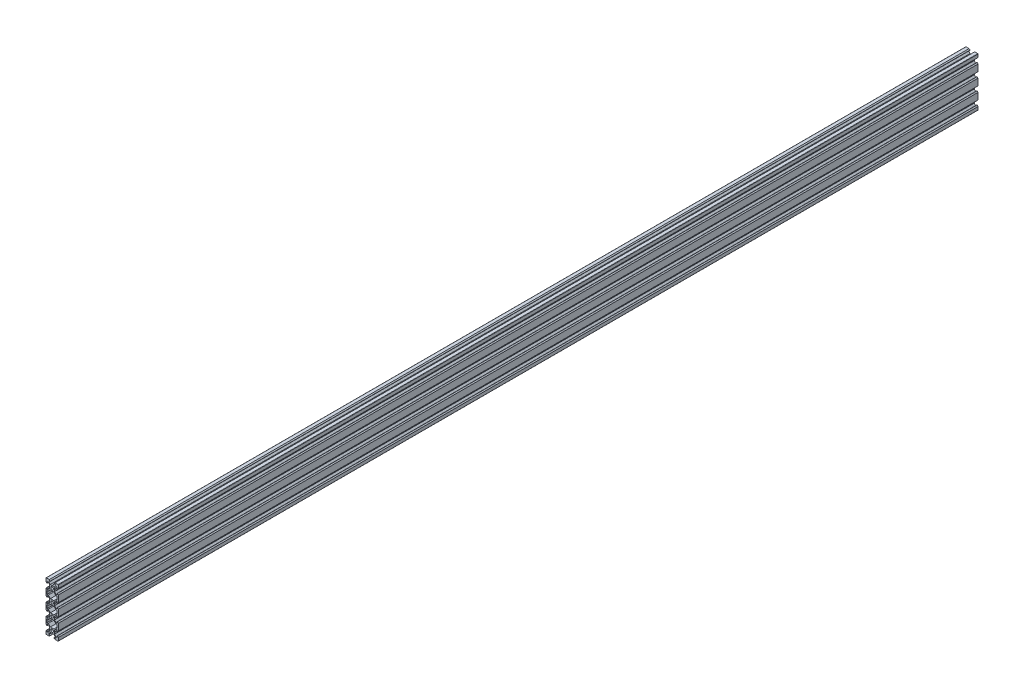
SolidWorks part; units mm, degrees
material "6061-T6 (SS)"
ref_plane "Front Plane" through (0, 0, 0) normal (0, 0, 1) x (1, 0, 0)
ref_plane "Top Plane" through (0, 0, 0) normal (0, 1, 0) x (1, 0, 0)
ref_plane "Right Plane" through (0, 0, 0) normal (1, 0, 0) x (0, 0, -1)
sketch "Sketch1" plane through (0, 0, 0) normal (0, 0, 1) x (1, 0, 0)
  line L0 (0, 0) -> (10, 0) construction
  line L1 (9.5, -40) -> (-9.5, -40)
  line L2 (10, -39.5) -> (10, 39.5)
  line L3 (9.5, 40) -> (-9.5, 40)
  line L4 (-10, -39.5) -> (-10, 39.5)
  line L5 (10, -40) -> (-10, 40) construction
  line L6 (10, 40) -> (-10, -40) construction
  circle A0 centre (0, 30) radius 2.1
  circle A1 centre (0, 10) radius 2.1
  circle A2 centre (0, -10) radius 2.1
  circle A3 centre (0, -30) radius 2.1
  arc A4 (-9.5, -40) -> (-10, -39.5) centre (-9.5, -39.5) cw
  arc A5 (9.5, -40) -> (10, -39.5) centre (9.5, -39.5) ccw
  arc A6 (10, 39.5) -> (9.5, 40) centre (9.5, 39.5) ccw
  arc A7 (-9.5, 40) -> (-10, 39.5) centre (-9.5, 39.5) ccw
  point P0 (0, 0)
  line B0 (0, 30) -> (0, 40) construction
  line B1 (0, 33.69) -> (-0.21, 33.9)
  line B2 (-0.21, 33.9) -> (-2.8393, 33.9)
  line B3 (-2.8393, 33.9) -> (-5.5, 36.5607)
  line B4 (-5.5, 36.5607) -> (-5.5, 38.2)
  line B5 (-5.5, 38.2) -> (-3.125, 38.2)
  line B6 (-3.125, 38.2) -> (-3.125, 38.545)
  line B7 (-3.125, 38.545) -> (-4.58, 40)
  line B8 (-4.58, 40) -> (4.58, 40)
  line B9 (0, 30) -> (-5.9132, 35.9132) construction
  line B10 (3.125, 38.545) -> (4.58, 40)
  line B11 (3.125, 38.2) -> (3.125, 38.545)
  line B12 (5.5, 38.2) -> (3.125, 38.2)
  line B13 (5.5, 36.5607) -> (5.5, 38.2)
  line B14 (2.8393, 33.9) -> (5.5, 36.5607)
  line B15 (0.21, 33.9) -> (2.8393, 33.9)
  line B16 (0, 33.69) -> (0.21, 33.9)
  line B17 (0, 30) -> (-10, 30) construction
  line B18 (-3.69, 30) -> (-3.9, 29.79)
  line B19 (-3.9, 29.79) -> (-3.9, 27.1607)
  line B20 (-3.9, 27.1607) -> (-6.5607, 24.5)
  line B21 (-6.5607, 24.5) -> (-8.2, 24.5)
  line B22 (-8.2, 24.5) -> (-8.2, 26.875)
  line B23 (-8.2, 26.875) -> (-8.545, 26.875)
  line B24 (-8.545, 26.875) -> (-10, 25.42)
  line B25 (-10, 25.42) -> (-10, 34.58)
  line B26 (0, 30) -> (-5.9132, 24.0868) construction
  line B27 (-8.545, 33.125) -> (-10, 34.58)
  line B28 (-8.2, 33.125) -> (-8.545, 33.125)
  line B29 (-8.2, 35.5) -> (-8.2, 33.125)
  line B30 (-6.5607, 35.5) -> (-8.2, 35.5)
  line B31 (-3.9, 32.8393) -> (-6.5607, 35.5)
  line B32 (-3.9, 30.21) -> (-3.9, 32.8393)
  line B33 (-3.69, 30) -> (-3.9, 30.21)
  line B34 (0, 10) -> (-10, 10) construction
  line B35 (-3.69, 10) -> (-3.9, 9.79)
  line B36 (-3.9, 9.79) -> (-3.9, 7.1607)
  line B37 (-3.9, 7.1607) -> (-6.5607, 4.5)
  line B38 (-6.5607, 4.5) -> (-8.2, 4.5)
  line B39 (-8.2, 4.5) -> (-8.2, 6.875)
  line B40 (-8.2, 6.875) -> (-8.545, 6.875)
  line B41 (-8.545, 6.875) -> (-10, 5.42)
  line B42 (-10, 5.42) -> (-10, 14.58)
  line B43 (0, 10) -> (-5.9132, 4.0868) construction
  line B44 (-8.545, 13.125) -> (-10, 14.58)
  line B45 (-8.2, 13.125) -> (-8.545, 13.125)
  line B46 (-8.2, 15.5) -> (-8.2, 13.125)
  line B47 (-6.5607, 15.5) -> (-8.2, 15.5)
  line B48 (-3.9, 12.8393) -> (-6.5607, 15.5)
  line B49 (-3.9, 10.21) -> (-3.9, 12.8393)
  line B50 (-3.69, 10) -> (-3.9, 10.21)
  line B51 (0, -10) -> (-10, -10) construction
  line B52 (-3.69, -10) -> (-3.9, -10.21)
  line B53 (-3.9, -10.21) -> (-3.9, -12.8393)
  line B54 (-3.9, -12.8393) -> (-6.5607, -15.5)
  line B55 (-6.5607, -15.5) -> (-8.2, -15.5)
  line B56 (-8.2, -15.5) -> (-8.2, -13.125)
  line B57 (-8.2, -13.125) -> (-8.545, -13.125)
  line B58 (-8.545, -13.125) -> (-10, -14.58)
  line B59 (-10, -14.58) -> (-10, -5.42)
  line B60 (0, -10) -> (-5.9132, -15.9132) construction
  line B61 (-8.545, -6.875) -> (-10, -5.42)
  line B62 (-8.2, -6.875) -> (-8.545, -6.875)
  line B63 (-8.2, -4.5) -> (-8.2, -6.875)
  line B64 (-6.5607, -4.5) -> (-8.2, -4.5)
  line B65 (-3.9, -7.1607) -> (-6.5607, -4.5)
  line B66 (-3.9, -9.79) -> (-3.9, -7.1607)
  line B67 (-3.69, -10) -> (-3.9, -9.79)
  line B68 (0, -30) -> (-10, -30) construction
  line B69 (-3.69, -30) -> (-3.9, -30.21)
  line B70 (-3.9, -30.21) -> (-3.9, -32.8393)
  line B71 (-3.9, -32.8393) -> (-6.5607, -35.5)
  line B72 (-6.5607, -35.5) -> (-8.2, -35.5)
  line B73 (-8.2, -35.5) -> (-8.2, -33.125)
  line B74 (-8.2, -33.125) -> (-8.545, -33.125)
  line B75 (-8.545, -33.125) -> (-10, -34.58)
  line B76 (-10, -34.58) -> (-10, -25.42)
  line B77 (0, -30) -> (-5.9132, -35.9132) construction
  line B78 (-8.545, -26.875) -> (-10, -25.42)
  line B79 (-8.2, -26.875) -> (-8.545, -26.875)
  line B80 (-8.2, -24.5) -> (-8.2, -26.875)
  line B81 (-6.5607, -24.5) -> (-8.2, -24.5)
  line B82 (-3.9, -27.1607) -> (-6.5607, -24.5)
  line B83 (-3.9, -29.79) -> (-3.9, -27.1607)
  line B84 (-3.69, -30) -> (-3.9, -29.79)
  line B85 (0, -30) -> (0, -40) construction
  line B86 (0, -33.69) -> (0.21, -33.9)
  line B87 (0.21, -33.9) -> (2.8393, -33.9)
  line B88 (2.8393, -33.9) -> (5.5, -36.5607)
  line B89 (5.5, -36.5607) -> (5.5, -38.2)
  line B90 (5.5, -38.2) -> (3.125, -38.2)
  line B91 (3.125, -38.2) -> (3.125, -38.545)
  line B92 (3.125, -38.545) -> (4.58, -40)
  line B93 (4.58, -40) -> (-4.58, -40)
  line B94 (0, -30) -> (5.9132, -35.9132) construction
  line B95 (-3.125, -38.545) -> (-4.58, -40)
  line B96 (-3.125, -38.2) -> (-3.125, -38.545)
  line B97 (-5.5, -38.2) -> (-3.125, -38.2)
  line B98 (-5.5, -36.5607) -> (-5.5, -38.2)
  line B99 (-2.8393, -33.9) -> (-5.5, -36.5607)
  line B100 (-0.21, -33.9) -> (-2.8393, -33.9)
  line B101 (0, -33.69) -> (-0.21, -33.9)
  line B102 (0, -30) -> (10, -30) construction
  line B103 (3.69, -30) -> (3.9, -29.79)
  line B104 (3.9, -29.79) -> (3.9, -27.1607)
  line B105 (3.9, -27.1607) -> (6.5607, -24.5)
  line B106 (6.5607, -24.5) -> (8.2, -24.5)
  line B107 (8.2, -24.5) -> (8.2, -26.875)
  line B108 (8.2, -26.875) -> (8.545, -26.875)
  line B109 (8.545, -26.875) -> (10, -25.42)
  line B110 (10, -25.42) -> (10, -34.58)
  line B111 (0, -30) -> (5.9132, -24.0868) construction
  line B112 (8.545, -33.125) -> (10, -34.58)
  line B113 (8.2, -33.125) -> (8.545, -33.125)
  line B114 (8.2, -35.5) -> (8.2, -33.125)
  line B115 (6.5607, -35.5) -> (8.2, -35.5)
  line B116 (3.9, -32.8393) -> (6.5607, -35.5)
  line B117 (3.9, -30.21) -> (3.9, -32.8393)
  line B118 (3.69, -30) -> (3.9, -30.21)
  line B119 (0, -10) -> (10, -10) construction
  line B120 (3.69, -10) -> (3.9, -9.79)
  line B121 (3.9, -9.79) -> (3.9, -7.1607)
  line B122 (3.9, -7.1607) -> (6.5607, -4.5)
  line B123 (6.5607, -4.5) -> (8.2, -4.5)
  line B124 (8.2, -4.5) -> (8.2, -6.875)
  line B125 (8.2, -6.875) -> (8.545, -6.875)
  line B126 (8.545, -6.875) -> (10, -5.42)
  line B127 (10, -5.42) -> (10, -14.58)
  line B128 (0, -10) -> (5.9132, -4.0868) construction
  line B129 (8.545, -13.125) -> (10, -14.58)
  line B130 (8.2, -13.125) -> (8.545, -13.125)
  line B131 (8.2, -15.5) -> (8.2, -13.125)
  line B132 (6.5607, -15.5) -> (8.2, -15.5)
  line B133 (3.9, -12.8393) -> (6.5607, -15.5)
  line B134 (3.9, -10.21) -> (3.9, -12.8393)
  line B135 (3.69, -10) -> (3.9, -10.21)
  line B136 (0, 10) -> (10, 10) construction
  line B137 (3.69, 10) -> (3.9, 10.21)
  line B138 (3.9, 10.21) -> (3.9, 12.8393)
  line B139 (3.9, 12.8393) -> (6.5607, 15.5)
  line B140 (6.5607, 15.5) -> (8.2, 15.5)
  line B141 (8.2, 15.5) -> (8.2, 13.125)
  line B142 (8.2, 13.125) -> (8.545, 13.125)
  line B143 (8.545, 13.125) -> (10, 14.58)
  line B144 (10, 14.58) -> (10, 5.42)
  line B145 (0, 10) -> (5.9132, 15.9132) construction
  line B146 (8.545, 6.875) -> (10, 5.42)
  line B147 (8.2, 6.875) -> (8.545, 6.875)
  line B148 (8.2, 4.5) -> (8.2, 6.875)
  line B149 (6.5607, 4.5) -> (8.2, 4.5)
  line B150 (3.9, 7.1607) -> (6.5607, 4.5)
  line B151 (3.9, 9.79) -> (3.9, 7.1607)
  line B152 (3.69, 10) -> (3.9, 9.79)
  line B153 (0, 30) -> (10, 30) construction
  line B154 (3.69, 30) -> (3.9, 30.21)
  line B155 (3.9, 30.21) -> (3.9, 32.8393)
  line B156 (3.9, 32.8393) -> (6.5607, 35.5)
  line B157 (6.5607, 35.5) -> (8.2, 35.5)
  line B158 (8.2, 35.5) -> (8.2, 33.125)
  line B159 (8.2, 33.125) -> (8.545, 33.125)
  line B160 (8.545, 33.125) -> (10, 34.58)
  line B161 (10, 34.58) -> (10, 25.42)
  line B162 (0, 30) -> (5.9132, 35.9132) construction
  line B163 (8.545, 26.875) -> (10, 25.42)
  line B164 (8.2, 26.875) -> (8.545, 26.875)
  line B165 (8.2, 24.5) -> (8.2, 26.875)
  line B166 (6.5607, 24.5) -> (8.2, 24.5)
  line B167 (3.9, 27.1607) -> (6.5607, 24.5)
  line B168 (3.9, 29.79) -> (3.9, 27.1607)
  line B169 (3.69, 30) -> (3.9, 29.79)
  line B170 (-8.2, 17.3) -> (-8.2, 22.7)
  line B171 (-8.2, 22.7) -> (-6.2393, 22.7)
  line B172 (-6.2393, 22.7) -> (-2.8393, 26.1)
  line B173 (-2.8393, 26.1) -> (2.8393, 26.1)
  line B174 (0, 26.1) -> (0, 20) construction
  line B175 (0, 20) -> (-8.2, 20) construction
  line B176 (6.2393, 22.7) -> (2.8393, 26.1)
  line B177 (8.2, 22.7) -> (6.2393, 22.7)
  line B178 (8.2, 17.3) -> (8.2, 22.7)
  line B179 (8.2, 17.3) -> (6.2393, 17.3)
  line B180 (6.2393, 17.3) -> (2.8393, 13.9)
  line B181 (-2.8393, 13.9) -> (2.8393, 13.9)
  line B182 (-6.2393, 17.3) -> (-2.8393, 13.9)
  line B183 (-8.2, 17.3) -> (-6.2393, 17.3)
  line B184 (0, 26.1) -> (0, 30) construction
  line B185 (0, 30) -> (-5.0927, 24.9073) construction
  line B186 (-8.2, -2.7) -> (-8.2, 2.7)
  line B187 (-8.2, 2.7) -> (-6.2393, 2.7)
  line B188 (-6.2393, 2.7) -> (-2.8393, 6.1)
  line B189 (-2.8393, 6.1) -> (2.8393, 6.1)
  line B190 (0, 6.1) -> (0, 0) construction
  line B191 (0, 0) -> (-8.2, 0) construction
  line B192 (6.2393, 2.7) -> (2.8393, 6.1)
  line B193 (8.2, 2.7) -> (6.2393, 2.7)
  line B194 (8.2, -2.7) -> (8.2, 2.7)
  line B195 (8.2, -2.7) -> (6.2393, -2.7)
  line B196 (6.2393, -2.7) -> (2.8393, -6.1)
  line B197 (-2.8393, -6.1) -> (2.8393, -6.1)
  line B198 (-6.2393, -2.7) -> (-2.8393, -6.1)
  line B199 (-8.2, -2.7) -> (-6.2393, -2.7)
  line B200 (0, 6.1) -> (0, 10) construction
  line B201 (0, 10) -> (-5.0927, 4.9073) construction
  line B202 (-8.2, -22.7) -> (-8.2, -17.3)
  line B203 (-8.2, -17.3) -> (-6.2393, -17.3)
  line B204 (-6.2393, -17.3) -> (-2.8393, -13.9)
  line B205 (-2.8393, -13.9) -> (2.8393, -13.9)
  line B206 (0, -13.9) -> (0, -20) construction
  line B207 (0, -20) -> (-8.2, -20) construction
  line B208 (6.2393, -17.3) -> (2.8393, -13.9)
  line B209 (8.2, -17.3) -> (6.2393, -17.3)
  line B210 (8.2, -22.7) -> (8.2, -17.3)
  line B211 (8.2, -22.7) -> (6.2393, -22.7)
  line B212 (6.2393, -22.7) -> (2.8393, -26.1)
  line B213 (-2.8393, -26.1) -> (2.8393, -26.1)
  line B214 (-6.2393, -22.7) -> (-2.8393, -26.1)
  line B215 (-8.2, -22.7) -> (-6.2393, -22.7)
  line B216 (0, -13.9) -> (0, -10) construction
  line B217 (0, -10) -> (-5.0927, -15.0927) construction
  dimension "D5" = 4.2
  dimension "D6" = 0.5
  dimension "D1" = 20
  dimension "D2" = 80
  dimension "D3" = 20
  dimension "D4" = 20
sketch_block_instance "V Slot 1-4"
sketch_block "V Slot 1" parameters "D1"=10, "D2"=11, "D3"=4.3, "D4"=1.8, "D5"=0.21, "D6"=45, "D7"=9.16, "D8"=1.5, "D9"=6.25
sketch_block_instance "V Slot 1-5"
sketch_block_instance "V Slot 1-6"
sketch_block_instance "V Slot 1-7"
sketch_block_instance "V Slot 1-8"
sketch_block_instance "V Slot 1-9"
sketch_block_instance "V Slot 1-10"
sketch_block_instance "V Slot 1-11"
sketch_block_instance "V Slot 1-12"
sketch_block_instance "V Slot 1-13"
sketch_block_instance "Center Cutout 1-1"
sketch_block "Center Cutout 1" parameters "D1"=5.4, "D2"=12.2, "D3"=8.2, "D4"=45, "D5"=10, "D6"=1.5
sketch_block_instance "Center Cutout 1-2"
sketch_block_instance "Center Cutout 1-3"
extrude "Boss-Extrude1" add sketch "Sketch1" along normal blind 1500 contours B169 B154 B155 B156 B157 B158 B159 B160 L2 A6 L3 B10 B11 B12 B13 B14 B15 B16 B1 B2 B3 B4 B5 B6 B7 A7 L4 B27 B28 B29 B30 B31 B32 B33 B18 B19 B20 B21 B22 B23 B24 B44 B45 B46 B47 B48 B49 B50 B35
